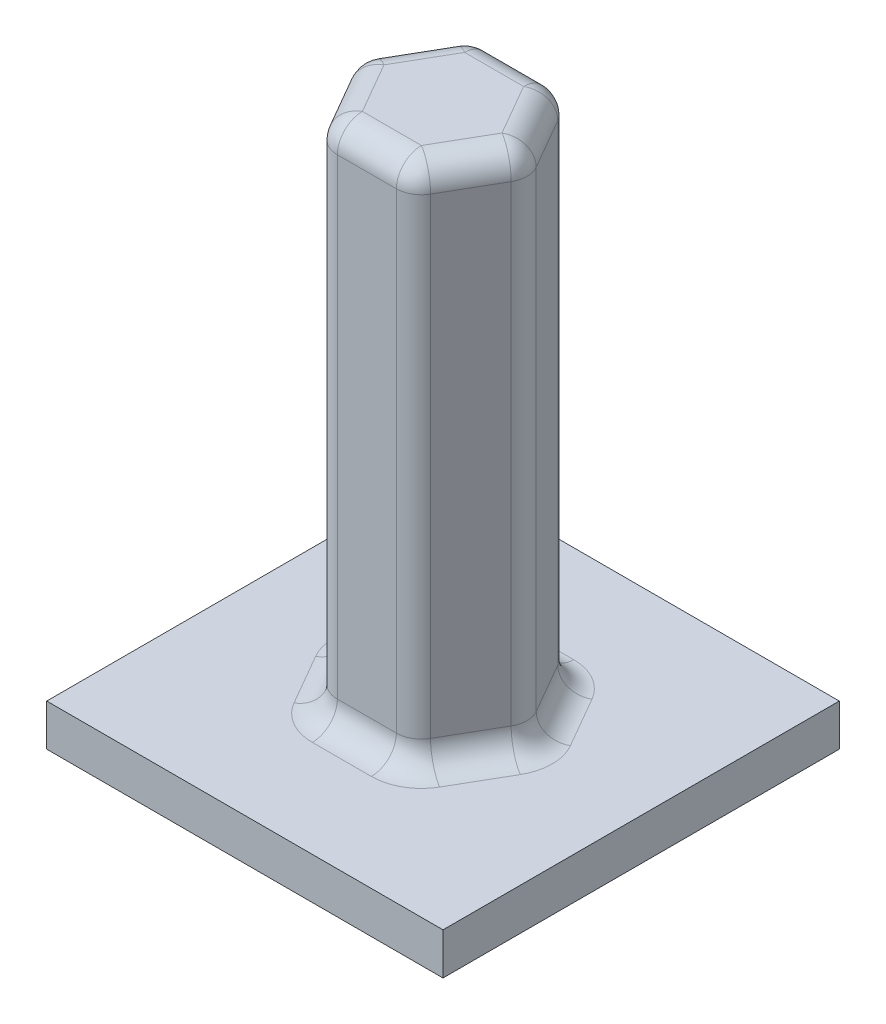
SolidWorks part; units mm, degrees
ref_plane "Alzado" through (0, 0, 0) normal (0, 0, 1) x (1, 0, 0)
ref_plane "Planta" through (0, 0, 0) normal (0, 1, 0) x (1, 0, 0)
ref_plane "Vista lateral" through (0, 0, 0) normal (1, 0, 0) x (0, 0, -1)
sketch "Croquis1" plane through (0, 0, 0) normal (0, 1, 0) x (1, 0, 0)
  line L1 (-9.5, -9.5) -> (9.5, -9.5)
  line L2 (-9.5, -9.5) -> (-9.5, 9.5)
  line L3 (-9.5, 9.5) -> (9.5, 9.5)
  line L4 (9.5, -9.5) -> (9.5, 9.5)
  line L5 (-9.5, -9.5) -> (9.5, 9.5) construction
  line L6 (-9.5, 9.5) -> (9.5, -9.5) construction
  point P0 (0, 0)
  dimension "D1" = 19
extrude "Saliente-Extruir1" add sketch "Croquis1" along normal blind 2
sketch "Croquis2" plane through (0, 2, 0) normal (0, 1, 0) x (1, 0, 0)
  line L1 (4.2147, 0) -> (2.1073, 3.65)
  line L2 (2.1073, 3.65) -> (-2.1073, 3.65)
  line L3 (-2.1073, 3.65) -> (-4.2147, 0)
  line L4 (-4.2147, 0) -> (-2.1073, -3.65)
  line L5 (-2.1073, -3.65) -> (2.1073, -3.65)
  line L6 (2.1073, -3.65) -> (4.2147, 0)
  circle A0 centre (0, 0) radius 3.65 construction
  dimension "D1" = 7.3
extrude "Saliente-Extruir2" add sketch "Croquis2" along normal blind 25
fillet "Redondeo1" radius 1.2 18 edges at (-3.161, 27, -1.825) (-3.161, 2, -1.825) (0, 27, -3.65) (-2.1073, 14.5, -3.65) (0, 2, -3.65) (3.161, 27, -1.825) (2.1073, 14.5, -3.65) (3.161, 2, -1.825) (3.161, 27, 1.825) (4.2147, 14.5, 0) (3.161, 2, 1.825) (0, 27, 3.65) (2.1073, 14.5, 3.65) (0, 2, 3.65) (-4.2147, 14.5, 0) (-3.161, 27, 1.825) (-2.1073, 14.5, 3.65) (-3.161, 2, 1.825)
